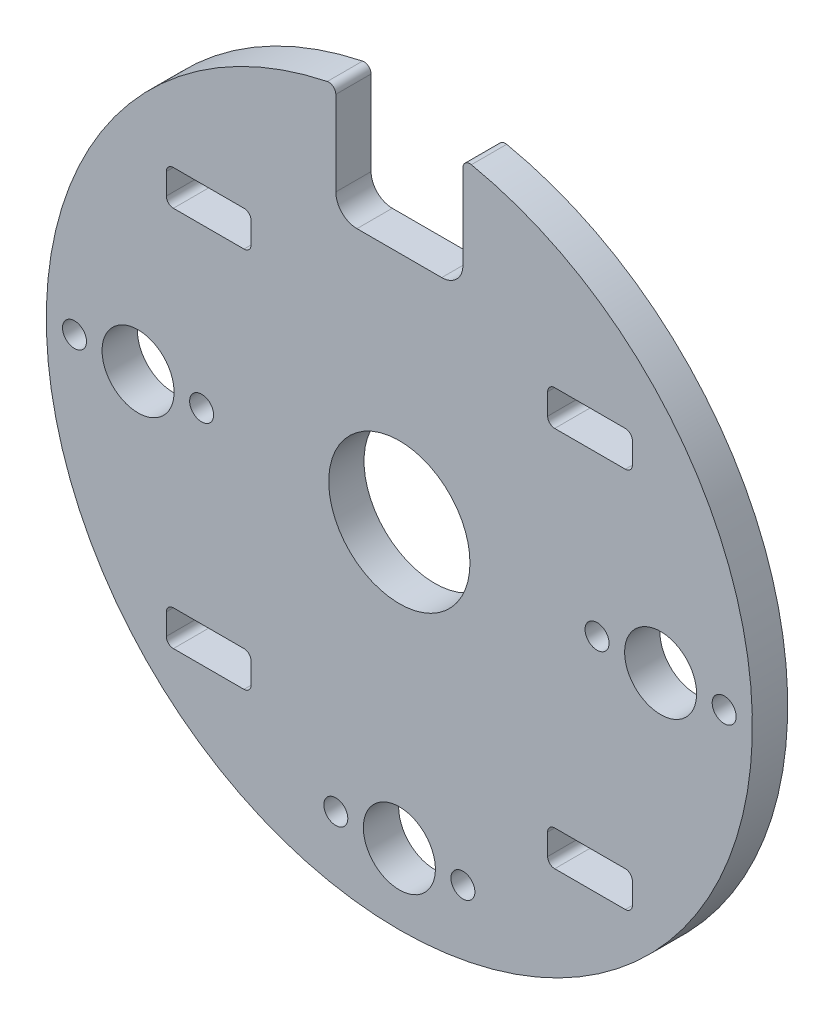
SolidWorks part; units mm, degrees
material "Acrylic (Medium-high impact)"
ref_plane "Front Plane" through (0, 0, 0) normal (0, 0, 1) x (1, 0, 0)
ref_plane "Top Plane" through (0, 0, 0) normal (0, 1, 0) x (1, 0, 0)
ref_plane "Right Plane" through (0, 0, 0) normal (1, 0, 0) x (0, 0, -1)
sketch "Sketch1" plane through (0, 0, 0) normal (0, 0, 1) x (1, 0, 0)
  circle A0 centre (0, 0) radius 50
  dimension "D1" = 100
extrude "Boss-Extrude1" add sketch "Sketch1" along normal blind 5
hole_wizard "Ø10.2 (10.2) Diameter Hole1" positions "Sketch5" profile "Sketch6" hole size "Ø10.2" standard "ISO"
sketch "Sketch5" plane through (0, 0, 0) normal (0, 0, -1) x (-1, 0, 0)
  point P4 (37, 0)
  point P17 (-37, 0)
  point P21 (0, -37) [skipped]
  point P23 (0, -40)
  dimension "D1" = 3
  dimension "D3" = 37
sketch "Sketch6" plane through (-37, 0, 0) normal (1, 0, 0) x (0, 1, 0)
  line L0 (0, 0) -> (0, 5)
  line L1 (0, 5) -> (5.1, 5)
  line L2 (5.1, 5) -> (5.1, 0)
  line L5 (5.1, 0) -> (0, 0)
  line L11 (0, -6.35) -> (0, 107.95) construction
  dimension "Thru Hole Dia." = 10.2
  dimension "Thru Hole Depth" = 5
hole_wizard "M3 Clearance Hole1" positions "Sketch7" profile "Sketch8" hole size "M3" standard "ISO" end condition through all
sketch "Sketch7" plane through (0, 0, 5) normal (0, 0, 1) x (1, 0, 0)
  circle A0 centre (37, 0) radius 5.1 construction
  circle A1 centre (0, -40) radius 5.1 construction
  point P0 (46, 0)
  point P2 (28, 0)
  point P11 (9, -40)
  point P13 (-9, -40)
  point P46 (-46, 0)
  point P47 (-28, 0)
  dimension "D2" = 9
  dimension "D1" = 9
  dimension "D4" = 9
  dimension "D5" = 9
  dimension "D6" = 2
  dimension "D3" = 40
sketch "Sketch8" plane through (46, 0, 5) normal (1, 0, 0) x (0, -1, 0)
  line L0 (0, 0) -> (0, 5)
  line L1 (0, 5) -> (1.7, 5)
  line L2 (1.7, 5) -> (1.7, 0)
  line L5 (1.7, 0) -> (0, 0)
  line L11 (0, -6.35) -> (0, 107.95) construction
  dimension "Thru Hole Dia." = 3.4
  dimension "Thru Hole Depth" = 5
sketch "Sketch11" plane through (0, 0, 5) normal (0, 0, 1) x (1, 0, 0)
  line L0 (-8.632, -2) -> (24.666, -2) construction
  line L1 (0, 0) -> (0, 21.5678) construction
  line L2 (22, 22.5) -> (32, 22.5)
  line L3 (21, 23.5) -> (21, 26.5)
  line L4 (22, 27.5) -> (32, 27.5)
  line L5 (33, 23.5) -> (33, 26.5)
  line L6 (-22, 27.5) -> (-32, 27.5)
  line L7 (-33, 23.5) -> (-33, 26.5)
  line L8 (-22, 22.5) -> (-32, 22.5)
  line L9 (-21, 23.5) -> (-21, 26.5)
  line L18 (-21, -27.5) -> (-21, -30.5)
  line L19 (-22, -26.5) -> (-32, -26.5)
  line L20 (-33, -27.5) -> (-33, -30.5)
  line L21 (-22, -31.5) -> (-32, -31.5)
  line L22 (22, -31.5) -> (32, -31.5)
  line L23 (33, -27.5) -> (33, -30.5)
  line L24 (22, -26.5) -> (32, -26.5)
  line L25 (21, -27.5) -> (21, -30.5)
  arc A4 (33, 26.5) -> (32, 27.5) centre (32, 26.5) ccw
  arc A5 (21, 26.5) -> (22, 27.5) centre (22, 26.5) cw
  arc A6 (21, 23.5) -> (22, 22.5) centre (22, 23.5) ccw
  arc A7 (33, 23.5) -> (32, 22.5) centre (32, 23.5) cw
  arc A8 (-33, 23.5) -> (-32, 22.5) centre (-32, 23.5) ccw
  arc A9 (-32, 27.5) -> (-33, 26.5) centre (-32, 26.5) ccw
  arc A10 (-22, 27.5) -> (-21, 26.5) centre (-22, 26.5) cw
  arc A11 (-22, 22.5) -> (-21, 23.5) centre (-22, 23.5) ccw
  arc A12 (-32, -26.5) -> (-33, -27.5) centre (-32, -27.5) ccw
  arc A13 (-33, -30.5) -> (-32, -31.5) centre (-32, -30.5) ccw
  arc A14 (-22, -31.5) -> (-21, -30.5) centre (-22, -30.5) ccw
  arc A15 (-21, -27.5) -> (-22, -26.5) centre (-22, -27.5) ccw
  arc A16 (22, -26.5) -> (21, -27.5) centre (22, -27.5) ccw
  arc A17 (21, -30.5) -> (22, -31.5) centre (22, -30.5) ccw
  arc A18 (33, -30.5) -> (32, -31.5) centre (32, -30.5) cw
  arc A19 (33, -27.5) -> (32, -26.5) centre (32, -27.5) ccw
  point P24 (33, 27.5)
  point P27 (21, 27.5)
  point P30 (21, 22.5)
  point P33 (33, 22.5)
  point P36 (-33, 22.5)
  point P39 (-33, 27.5)
  point P42 (-21, 27.5)
  point P45 (-21, 22.5)
  point P48 (-33, -26.5)
  point P51 (-33, -31.5)
  point P54 (-21, -31.5)
  point P57 (-21, -26.5)
  point P60 (21, -26.5)
  point P63 (21, -31.5)
  point P66 (33, -31.5)
  point P69 (33, -26.5)
  dimension "D1" = 27.5
  dimension "D4" = 12
  dimension "D6" = 1
  dimension "D7" = 1
  dimension "D8" = 1
  dimension "D2" = 21
  dimension "D3" = 5
  dimension "D5" = 2
extrude "Cut-Extrude2" cut sketch "Sketch11" against normal blind 5
ref_plane "Plane2" through (0, -2, 0) normal (0, 1, 0) x (1, 0, 0)
sketch "Sketch12" plane through (0, 0, 5) normal (0, 0, 1) x (1, 0, 0)
  line L0 (0, 0) -> (0, 40) construction
  line L1 (0, 0) -> (17.7545, 0) construction
  line L3 (-6, 33) -> (6, 33)
  line L4 (-9, 36) -> (-9, 50)
  line L5 (-9, 50) -> (9, 50)
  line L6 (9, 36) -> (9, 50)
  arc A0 (-9, 36) -> (-6, 33) centre (-6, 36) ccw
  arc A1 (9, 36) -> (6, 33) centre (6, 36) cw
  point P9 (0, 33)
  point P11 (-9, 33)
  dimension "D1" = 3
  dimension "D2" = 90
  dimension "D3" = 40
  dimension "D4" = 33
  dimension "D5" = 17
  dimension "D6" = 18
extrude "Cut-Extrude3" cut sketch "Sketch12" against normal blind 10
fillet "Fillet1" radius 1 2 edges at (9, 49.1833, 2.5) (-9, 49.1833, 2.5)
sketch "Sketch13" plane through (0, 0, 5) normal (0, 0, 1) x (1, 0, 0)
  circle A0 centre (0, 0) radius 10
  dimension "D1" = 20
extrude "Cut-Extrude4" cut sketch "Sketch13" against normal blind 10
